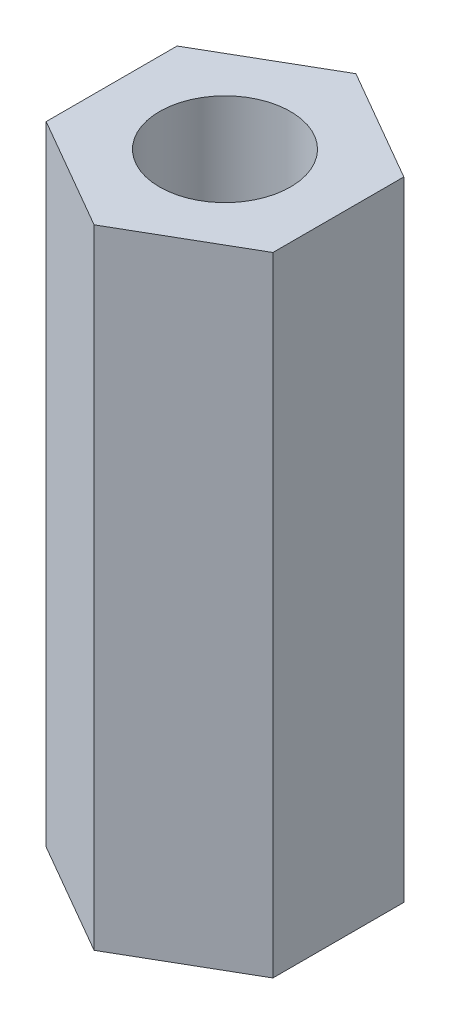
SolidWorks part; units mm, degrees
ref_plane "Face" through (0, 0, 0) normal (0, 0, 1) x (1, 0, 0)
ref_plane "Dessus" through (0, 0, 0) normal (0, 1, 0) x (1, 0, 0)
ref_plane "Droite" through (0, 0, 0) normal (1, 0, 0) x (0, 0, -1)
sketch "Esquisse1" plane through (0, 0, 0) normal (0, 1, 0) x (1, 0, 0)
  line L0 (0, 0) -> (0, 5.5688) construction
  line L1 (0, 5) -> (-4.3301, 2.5)
  line L2 (-4.3301, 2.5) -> (-4.3301, -2.5)
  line L3 (-4.3301, -2.5) -> (0, -5)
  line L4 (0, -5) -> (4.3301, -2.5)
  line L5 (4.3301, -2.5) -> (4.3301, 2.5)
  line L6 (4.3301, 2.5) -> (0, 5)
  circle A0 centre (0, 0) radius 4.3301 construction
  circle A1 centre (0, 0) radius 2.5
  dimension "D1" = 10
  dimension "D2" = 5
extrude "Extrusion1" add sketch "Esquisse1" along normal blind 24
